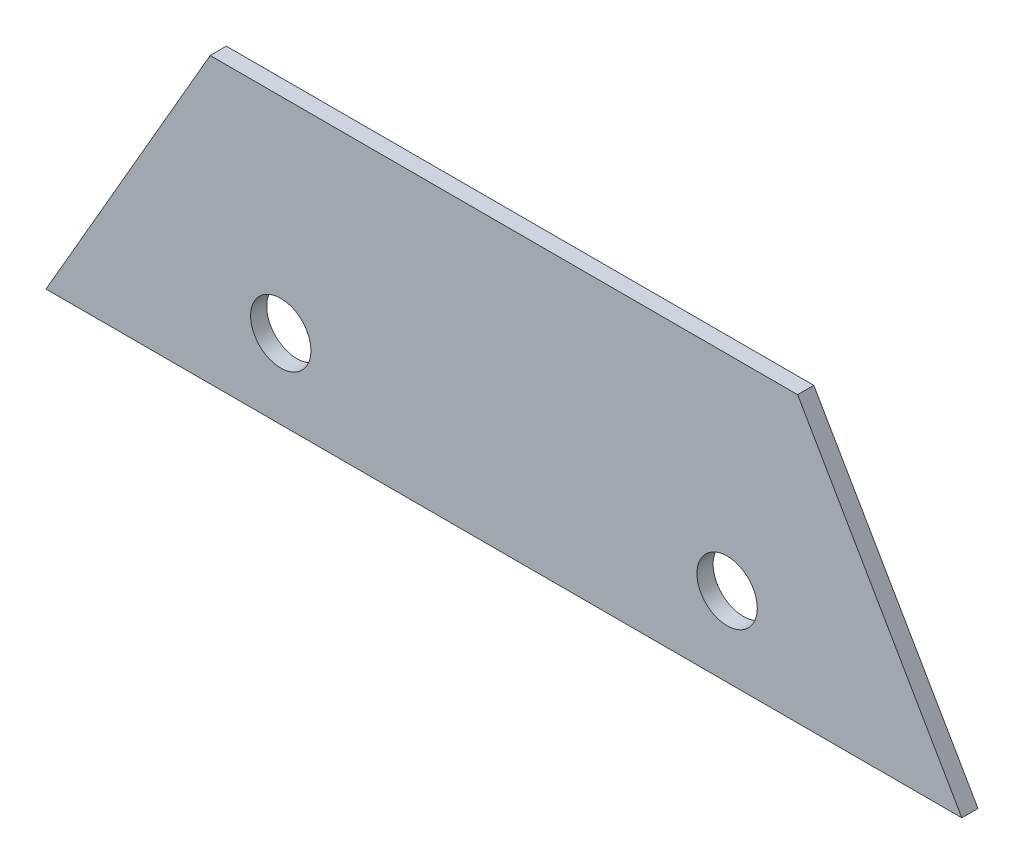
SolidWorks part; units mm, degrees
material "Pine"
ref_plane "Front Plane" through (0, 0, 0) normal (0, 0, 1) x (1, 0, 0)
ref_plane "Top Plane" through (0, 0, 0) normal (0, 1, 0) x (1, 0, 0)
ref_plane "Right Plane" through (0, 0, 0) normal (1, 0, 0) x (0, 0, -1)
sketch "Sketch1" plane through (0, 0, 0) normal (0, 0, 1) x (1, 0, 0)
  line L0 (-337.1149, -583.9002) -> (-216.2389, -374.5368)
  line L1 (-216.2389, -374.5368) -> (216.2389, -374.5368)
  line L2 (216.2389, -374.5368) -> (337.1149, -583.9002)
  line L3 (337.1149, -583.9002) -> (-337.1149, -583.9002)
  line L4 (-337.1149, -583.9002) -> (337.1149, -583.9002) construction
  line L5 (-216.2389, -374.5368) -> (-337.1149, -583.9002) construction
  line L6 (216.2389, -374.5368) -> (-216.2389, -374.5368) construction
  line L7 (337.1149, -583.9002) -> (216.2389, -374.5368) construction
extrude "Boss-Extrude1" add sketch "Sketch1" against normal up to surface (11.9063 mm away)
sketch "Sketch2" plane through (0, 0, 0) normal (0, 0, 1) x (1, 0, 0)
  circle A0 centre (-164.3095, -525.6072) radius 22.225
  circle A1 centre (164.3095, -525.6072) radius 22.225
  circle A2 centre (-164.3095, -525.6072) radius 22.225 construction
  circle A3 centre (164.3095, -525.6072) radius 22.225 construction
extrude "Cut-Extrude1" cut sketch "Sketch2" against normal through all
